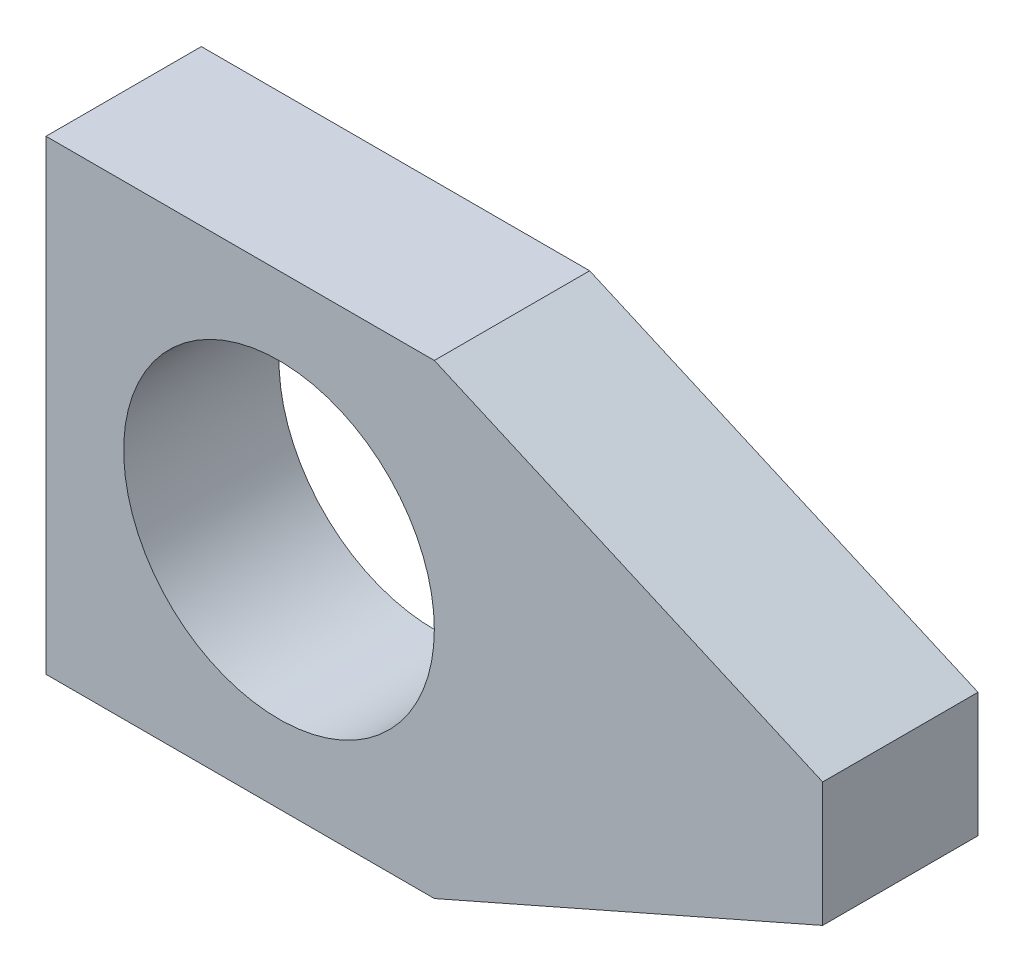
SolidWorks part; units mm, degrees
ref_plane "Front Plane" through (0, 0, 0) normal (0, 0, 1) x (1, 0, 0)
ref_plane "Top Plane" through (0, 0, 0) normal (0, 1, 0) x (1, 0, 0)
ref_plane "Right Plane" through (0, 0, 0) normal (1, 0, 0) x (0, 0, -1)
sketch "Sketch1" plane through (0, 0, 0) normal (0, 0, 1) x (1, 0, 0)
  line L0 (-15, 0) -> (0, 0) construction
  line L1 (-15, 15) -> (10, 15)
  line L2 (-15, 15) -> (-15, -15)
  line L3 (-15, -15) -> (10, -15)
  line L4 (35, 4) -> (35, -4)
  line L5 (0, 0) -> (0, 15) construction
  line L6 (10, -15) -> (35, -4)
  line L7 (10, 15) -> (35, 4)
  circle A0 centre (0, 0) radius 10
  dimension "D1" = 20
  dimension "D2" = 30
  dimension "D3" = 50
  dimension "D4" = 25
  dimension "D5" = 8
extrude "Boss-Extrude1" add sketch "Sketch1" along normal blind 10
